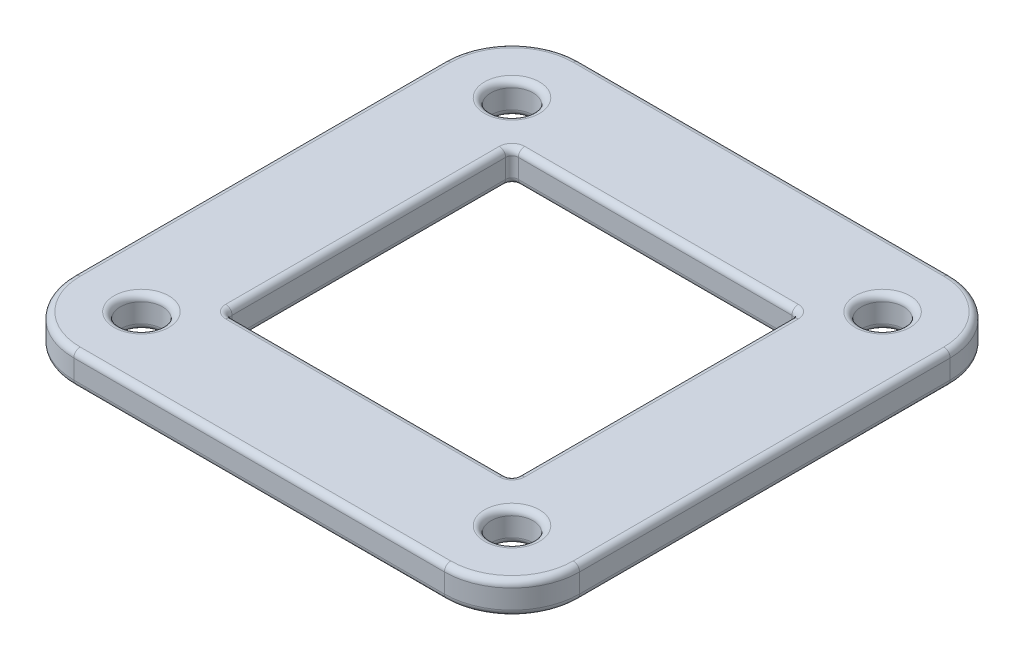
SolidWorks part; units mm, degrees
ref_plane "Front Plane" through (0, 0, 0) normal (0, 0, 1) x (1, 0, 0)
ref_plane "Top Plane" through (0, 0, 0) normal (0, 1, 0) x (1, 0, 0)
ref_plane "Right Plane" through (0, 0, 0) normal (1, 0, 0) x (0, 0, -1)
sketch "Main Sketch" plane through (0, 0, 0) normal (0, 1, 0) x (1, 0, 0)
  line L0 (-19.875, -19.875) -> (19.875, 19.875) construction
  line L1 (-19.875, 19.875) -> (19.875, 19.875)
  line L2 (-19.875, 19.875) -> (-19.875, -19.875)
  line L3 (-19.875, -19.875) -> (19.875, -19.875)
  line L4 (19.875, 19.875) -> (19.875, -19.875)
  point P4 (0, 0)
  dimension "D1" = 39.75
extrude "Main Extrude" add sketch "Main Sketch" along normal mid plane 2.5
sketch "Hole Cuts Sketch" plane through (0, 0, 0) normal (0, 1, 0) x (1, 0, 0)
  line L0 (-19.875, -19.875) -> (19.875, 19.875) construction
  line L1 (19.875, -19.875) -> (-19.875, 19.875) construction
  line L3 (11.25, -11.25) -> (-11.25, -11.25)
  line L4 (-14.5625, -14.5625) -> (-14.5625, 14.5625) construction
  line L5 (-14.5625, -14.5625) -> (14.5625, -14.5625) construction
  line L6 (14.5625, -14.5625) -> (14.5625, 14.5625) construction
  line L7 (11.25, -11.25) -> (11.25, 11.25)
  line L8 (11.25, 11.25) -> (-11.25, 11.25)
  line L9 (-11.25, -11.25) -> (-11.25, 11.25)
  line L10 (11.25, -11.25) -> (-11.25, 11.25) construction
  line L11 (11.25, 11.25) -> (-11.25, -11.25) construction
  circle A6 centre (14.5625, 14.5625) radius 1.6563
  circle A7 centre (14.5625, -14.5625) radius 1.6563
  circle A8 centre (-14.5625, -14.5625) radius 1.6563
  circle A9 centre (-14.5625, 14.5625) radius 1.6563
  point P0 (0, 0)
  dimension "D6" = 3.3125
  dimension "D12" = 29.125
  dimension "D3" = 22.5
extrude "Hole Cuts" cut sketch "Hole Cuts Sketch" against normal through all both and the other way through all
fillet "Corner Fillet" radius 5.3125 4 edges at (-19.875, 0, -19.875) (-19.875, 0, 19.875) (19.875, 0, -19.875) (19.875, 0, 19.875)
fillet "Small Fillet" radius 0.5 36 edges at (-18.319, -1.25, 18.319) (0, -1.25, 19.875) (18.319, -1.25, 18.319) (19.875, -1.25, 0) (18.319, -1.25, -18.319) (0, -1.25, -19.875) (-18.319, -1.25, -18.319) (-19.875, -1.25, 0) (-14.5625, -1.25, 16.2188) (14.5625, -1.25, 16.2188) (14.5625, -1.25, -12.9063) (18.319, 1.25, -18.319) (19.875, 1.25, 0) (18.319, 1.25, 18.319) (0, 1.25, 19.875) (-18.319, 1.25, 18.319) (-19.875, 1.25, 0) (-18.319, 1.25, -18.319) (0, 1.25, -19.875) (-14.5625, 1.25, 16.2188) (14.5625, 1.25, 16.2188) (14.5625, 1.25, -12.9063) (11.25, -1.25, 0) (0, -1.25, 11.25) (-11.25, -1.25, 0) (0, -1.25, -11.25) (0, 1.25, 11.25) (11.25, 1.25, 0) (0, 1.25, -11.25) (-11.25, 1.25, 0) (-11.25, 0, 11.25) (11.25, 0, 11.25) (11.25, 0, -11.25) (-11.25, 0, -11.25) (-14.5625, -1.25, -12.9062) (-14.5625, 1.25, -12.9062)
equation "\"D1@Main Extrude\" = \"ARM Both Prop Seal Thickness\""
equation "\"D6@Hole Cuts Sketch\" = \"ARM Both Prop Plate Bolt Size\" + ( \"ALL Bolt Hole Off\" * \"ALL Horz Bolt Hole Off Scalar\" )"
equation "\"D12@Hole Cuts Sketch\" = ( ( ( ( \"ARM Both Nema Width\" + \"ARM Both Nema Wall Off\" ) / 2 ) + ( ( \"ARM Both Dia\" - ( \"ARM Both Nema Width\" + \"ARM Both Nema Wall Off\" ) ) / 4 ) ) * 2 ) - 2.0mm"
equation "\"D1@Corner Fillet\" = ( \"ARM Both Dia\" - \"D12@Hole Cuts Sketch\" ) / 2"
equation "\"D1@Small Fillet\" = \"ALL Small Fillet\""
equation "\"D1@Main Sketch\"= \"ARM Both Dia\""
equation "\"D3@Hole Cuts Sketch\"= \"ARM Both Nema Width\" + \"ARM Both Nema Wall Off\""
equation "\"ALL Big Fillet\"= 10.0mm"
equation "\"ALL Medium Fillet\"= 1.0mm"
equation "\"ALL Small Fillet\"= 0.5mm"
equation "\"BODY Rad\"= 82.5mm"
equation "\"BODY End Cut Rad\"= 72.5mm"
equation "\"BODY Height Ext\"= 27.5mm"
equation "\"BODY Bottom Cut Dist\"= 50.0mm"
equation "\"BODY Seal Thickness\"= 3.75mm"
equation "\"BODY Wall Extra Thickness\"= 2.5mm"
equation "\"BODY Bottom Extra Nut Wall\"= 7.5mm"
equation "\"ARM Both Dia\"= 39.75mm"
equation "\"ARM Both Length\"= 67.5mm"
equation "\"ARM Both Wire Hole Dia\"= 15.0mm"
equation "\"ARM Both Prop Seal Thickness\"= 2.5mm"
equation "\"ARM Both Brass Insert Dia\"= 4.875mm"
equation "\"ARM Both Bolt Cut Depth\"= 12.5mm"
equation "\"ARM Both Nema Bolt Off\"= 15.4mm"
equation "\"ARM Both Nema Bolt Depth\"= 2.5mm"
equation "\"ARM Both Nema Width\"= 20.0mm"
equation "\"ARM Both Nema Wall Off\"= 2.5mm"
equation "\"ARM Both Nema Center Dia 1\"= 17.0mm"
equation "\"ARM Both Nema Center Dia 2\"= 10.0mm"
equation "\"ARM Both Nema Bearing OD\"= 16.0mm"
equation "\"ARM Both Nema Bearing ID\"= 10.0mm"
equation "\"ARM Both Nema Bearing Thickness\"= 4.0mm"
equation "\"ARM Both Nema Height\"= 38.0mm"
equation "\"ARM Both Nema Shaft Dia\"= 4.0mm"
equation "\"ARM Both Nema Shaft Length\"= 10.0mm"
equation "\"ARM Both Nema Center Height\"= 1.5mm"
equation "\"ARM Rotating Bearing OD\"= 68.0mm"
equation "\"ARM Rotating Bearing ID\"= 40.0mm"
equation "\"ARM Rotating Bearing Thickness\"= 15.0mm"
equation "\"ARM Static Mount Dia\"= 65.0mm"
equation "\"ARM Static Bolt Off\"= 1.125mm"
equation "\"ALL Bolt Hole Off\"= 0.25mm"
equation "\"ALL Vert Bolt Hole Off Scalar\"= 0.5mm"
equation "\"ALL Horz Bolt Hole Off Scalar\"= 1.25mm"
equation "\"ALL Nut Size Off\"= 0.25mm"
equation "\"ALL Vert Nut Off Scalar\"= 0.5mm"
equation "\"ALL Horz Nut Off Scalar\"= 1.25mm"
equation "\"BODY Bolt Count\"= 12"
equation "\"BODY Bolt Size\"= 6"
equation "\"BODY Bolt Length\"= 22.0mm"
equation "\"BODY Bolt Head Dia\"= IIF ( \"BODY Bolt Size\" = 3 , 5.75mm , IIF ( \"BODY Bolt Size\" = 4 , 7.25mm , IIF ( \"BODY Bolt Size\" = 5 , 8.75mm , IIF ( \"BODY Bolt Size\" = 6 , 10.25mm , 5.75mm ) ) ) )"
equation "\"BODY Bolt Head Height\"= IIF ( \"BODY Bolt Size\" = 3 , 3.0mm , IIF ( \"BODY Bolt Size\" = 4 , 4.0mm , IIF ( \"BODY Bolt Size\" = 5 , 5.0mm , IIF ( \"BODY Bolt Size\" = 6 , 6.0mm , 3.0mm ) ) ) )"
equation "\"BODY Nut Width\"= IIF ( \"BODY Bolt Size\" = 3 , 5.5mm , IIF ( \"BODY Bolt Size\" = 4 , 7.0mm , IIF ( \"BODY Bolt Size\" = 5 , 8.0mm , IIF ( \"BODY Bolt Size\" = 6 , 10.0mm , 5.5mm ) ) ) )"
equation "\"BODY Nut Height\"= IIF ( \"BODY Bolt Size\" = 3 , 4.0mm , IIF ( \"BODY Bolt Size\" = 4 , 5.0mm , IIF ( \"BODY Bolt Size\" = 5 , 5.0mm , IIF ( \"BODY Bolt Size\" = 6 , 6.0mm , 4.0mm ) ) ) )"
equation "\"ARM Static Bolt Count\"= 8"
equation "\"ARM Static Bolt Size\"= 5"
equation "\"ARM Static Bolt Length\"= 20.0mm"
equation "\"ARM Static Bolt Head Dia\"= IIF ( \"ARM Static Bolt Size\" = 3 , 5.75mm , IIF ( \"ARM Static Bolt Size\" = 4 , 7.25mm , IIF ( \"ARM Static Bolt Size\" = 5 , 8.75mm , IIF ( \"ARM Static Bolt Size\" = 6 , 10.25mm , 5.75mm ) ) ) )"
equation "\"ARM Static Bolt Head Height\"= IIF ( \"ARM Static Bolt Size\" = 3 , 3.0mm , IIF ( \"ARM Static Bolt Size\" = 4 , 4.0mm , IIF ( \"ARM Static Bolt Size\" = 5 , 5.0mm , IIF ( \"ARM Static Bolt Size\" = 6 , 6.0mm , 3.0mm ) ) ) )"
equation "\"ARM Static Nut Width\"= IIF ( \"ARM Static Bolt Size\" = 3 , 5.5mm , IIF ( \"ARM Static Bolt Size\" = 4 , 7.0mm , IIF ( \"ARM Static Bolt Size\" = 5 , 8.0mm , IIF ( \"ARM Static Bolt Size\" = 6 , 10.0mm , 5.5mm ) ) ) )"
equation "\"ARM Static Nut Height\"= IIF ( \"ARM Static Bolt Size\" = 3 , 4.0mm , IIF ( \"ARM Static Bolt Size\" = 4 , 5.0mm , IIF ( \"ARM Static Bolt Size\" = 5 , 5.0mm , IIF ( \"ARM Static Bolt Size\" = 6 , 6.0mm , 4.0mm ) ) ) )"
equation "\"ARM Gear Width\"= 10.0mm"
equation "\"ARM Gear Width Off\"= 2.5mm"
equation "\"ARM Gear Bolt Count\"= 4"
equation "\"ARM Gear Rotation\"= 360.0deg"
equation "\"ARM Gear Bolt Size\"= 3"
equation "\"ARM Gear Bolt Length\"= 20.0mm"
equation "\"ARM Gear Bolt Head Dia\"= IIF ( \"ARM Static Bolt Size\" = 3 , 5.75mm , IIF ( \"ARM Static Bolt Size\" = 4 , 7.25mm , IIF ( \"ARM Static Bolt Size\" = 5 , 8.75mm , IIF ( \"ARM Static Bolt Size\" = 6 , 10.25mm , 5.75mm ) ) ) )"
equation "\"ARM Gear Bolt Head Height\"= IIF ( \"ARM Static Bolt Size\" = 3 , 3.0mm , IIF ( \"ARM Static Bolt Size\" = 4 , 4.0mm , IIF ( \"ARM Static Bolt Size\" = 5 , 5.0mm , IIF ( \"ARM Static Bolt Size\" = 6 , 6.0mm , 3.0mm ) ) ) )"
equation "\"ARM Gear Nut Width\"= IIF ( \"ARM Static Bolt Size\" = 3 , 5.5mm , IIF ( \"ARM Static Bolt Size\" = 4 , 7.0mm , IIF ( \"ARM Static Bolt Size\" = 5 , 8.0mm , IIF ( \"ARM Static Bolt Size\" = 6 , 10.0mm , 5.5mm ) ) ) )"
equation "\"ARM Gear Nut Height\"= IIF ( \"ARM Static Bolt Size\" = 3 , 4.0mm , IIF ( \"ARM Static Bolt Size\" = 4 , 5.0mm , IIF ( \"ARM Static Bolt Size\" = 5 , 5.0mm , IIF ( \"ARM Static Bolt Size\" = 6 , 6.0mm , 4.0mm ) ) ) )"
equation "\"ARM Both Prop Plate Bolt Size\"= 3"
equation "\"ARM Both Prop Plate Bolt Length\"= 16.0mm"
equation "\"ARM Both Prop Plate Bolt Head Dia\"= IIF ( \"ARM Both Prop Plate Bolt Size\" = 3 , 5.75mm , IIF ( \"ARM Both Prop Plate Bolt Size\" = 4 , 7.25mm , IIF ( \"ARM Both Prop Plate Bolt Size\" = 5 , 8.75mm , IIF ( \"ARM Both Prop Plate Bolt Size\" = 6 , 10.25mm , 5.75mm ) ) ) )"
equation "\"ARM Both Prop Plate Bolt Head Height\"= IIF ( \"ARM Both Prop Plate Bolt Size\" = 3 , 3.0mm , IIF ( \"ARM Both Prop Plate Bolt Size\" = 4 , 4.0mm , IIF ( \"ARM Both Prop Plate Bolt Size\" = 5 , 5.0mm , IIF ( \"ARM Both Prop Plate Bolt Size\" = 6 , 6.0mm , 3.0mm ) ) ) )"
equation "\"ARM Both Nema Bolt Size\"= 2"
equation "\"ARM Both Nema Bolt Head Dia\"= IIF ( \"ARM Both Nema Bolt Size\" = 3 , 5.75mm , IIF ( \"ARM Both Nema Bolt Size\" = 4 , 7.25mm , IIF ( \"ARM Both Nema Bolt Size\" = 5 , 8.75mm , IIF ( \"ARM Both Nema Bolt Size\" = 6 , 10.25mm , 5.75mm ) ) ) )"
equation "\"ARM Both Nema Bolt Head Height\"= IIF ( \"ARM Both Nema Bolt Size\" = 3 , 3.0mm , IIF ( \"ARM Both Nema Bolt Size\" = 4 , 4.0mm , IIF ( \"ARM Both Nema Bolt Size\" = 5 , 5.0mm , IIF ( \"ARM Both Nema Bolt Size\" = 6 , 6.0mm , 3.0mm ) ) ) )"
